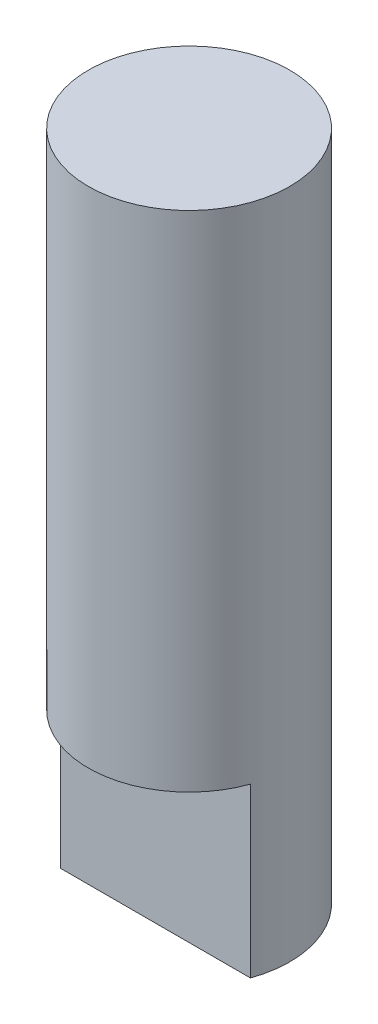
SolidWorks part; units mm, degrees
ref_plane "Front Plane" through (0, 0, 0) normal (0, 0, 1) x (1, 0, 0)
ref_plane "Top Plane" through (0, 0, 0) normal (0, 1, 0) x (1, 0, 0)
ref_plane "Right Plane" through (0, 0, 0) normal (1, 0, 0) x (0, 0, -1)
sketch "Sketch1" plane through (0, 0, 0) normal (0, 1, 0) x (1, 0, 0)
  circle A0 centre (0, 0) radius 3
  dimension "D1" = 6
extrude "Boss-Extrude1" add sketch "Sketch1" along normal blind 20
sketch "Sketch2" plane through (0, 0, 0) normal (0, -1, 0) x (1, 0, 0)
  line L0 (-2.8284, 1) -> (2.8284, 1)
  circle A0 centre (0, 0) radius 3 construction
  arc A1 (-2.8284, 1) -> (2.8284, 1) centre (0, 0) cw
  dimension "D2" = 3
  dimension "D1" = 1
extrude "Cut-Extrude1" cut sketch "Sketch2" against normal blind 5 contours L0 A1
